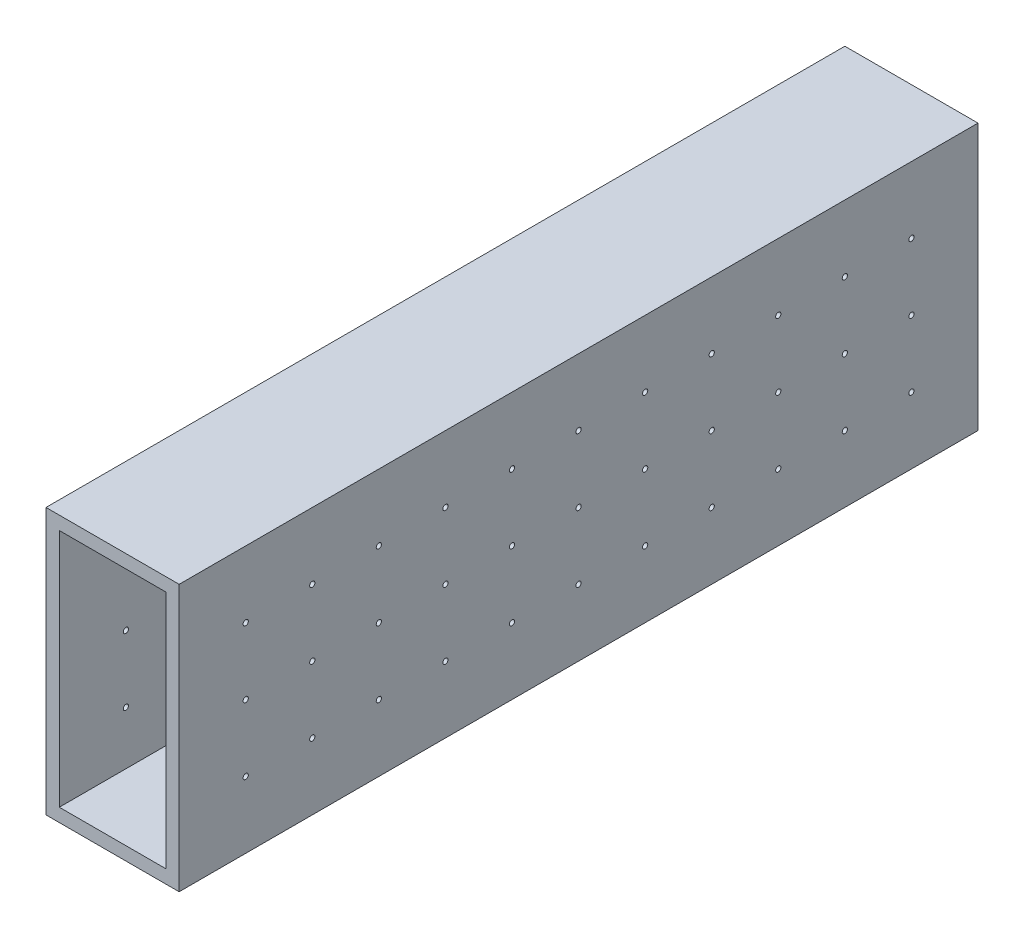
SolidWorks part; units mm, degrees
ref_plane "Front Plane" through (0, 0, 0) normal (0, 0, 1) x (1, 0, 0)
ref_plane "Top Plane" through (0, 0, 0) normal (0, 1, 0) x (1, 0, 0)
ref_plane "Right Plane" through (0, 0, 0) normal (1, 0, 0) x (0, 0, -1)
sketch "Sketch1" plane through (0, 0, 0) normal (0, 0, 1) x (1, 0, 0)
  line L1 (9.5125, 45.3382) -> (29.8325, 45.3382)
  line L2 (9.5125, 45.3382) -> (9.5125, -0.3818)
  line L3 (9.5125, -0.3818) -> (29.8325, -0.3818)
  line L4 (29.8325, 45.3382) -> (29.8325, -0.3818)
  line L5 (6.9725, 47.8782) -> (32.3725, 47.8782)
  line L6 (6.9725, 47.8782) -> (6.9725, -2.9218)
  line L7 (6.9725, -2.9218) -> (32.3725, -2.9218)
  line L8 (32.3725, 47.8782) -> (32.3725, -2.9218)
  dimension "D1" = 50.8
  dimension "D2" = 25.4
  dimension "D3" = 2.54
  dimension "D4" = 2.54
  dimension "D5" = 2.54
  dimension "D6" = 2.54
extrude "Boss-Extrude1" add sketch "Sketch1" along normal blind 152.4
sketch "Sketch2" plane through (32.3725, 0, 0) normal (1, 0, 0) x (0, 0, -1)
  line L0 (-152.4, -2.9218) -> (-152.4, 47.8782) construction
  line L1 (-152.4, 47.8782) -> (0, 47.8782) construction
  circle A0 centre (-139.7, 35.1782) radius 0.5
  circle A1 centre (-127, 35.1782) radius 0.5
  circle A2 centre (-114.3, 35.1782) radius 0.5
  circle A3 centre (-101.6, 35.1782) radius 0.5
  circle A4 centre (-88.9, 35.1782) radius 0.5
  circle A5 centre (-76.2, 35.1782) radius 0.5
  circle A6 centre (-63.5, 35.1782) radius 0.5
  circle A7 centre (-50.8, 35.1782) radius 0.5
  circle A8 centre (-38.1, 35.1782) radius 0.5
  circle A9 centre (-25.4, 35.1782) radius 0.5
  circle A10 centre (-12.7, 35.1782) radius 0.5
  circle A11 centre (-127, 22.4782) radius 0.5
  circle A12 centre (-114.3, 22.4782) radius 0.5
  circle A13 centre (-101.6, 22.4782) radius 0.5
  circle A14 centre (-88.9, 22.4782) radius 0.5
  circle A15 centre (-76.2, 22.4782) radius 0.5
  circle A16 centre (-63.5, 22.4782) radius 0.5
  circle A17 centre (-50.8, 22.4782) radius 0.5
  circle A18 centre (-38.1, 22.4782) radius 0.5
  circle A19 centre (-25.4, 22.4782) radius 0.5
  circle A20 centre (-12.7, 22.4782) radius 0.5
  circle A21 centre (-127, 9.7782) radius 0.5
  circle A22 centre (-114.3, 9.7782) radius 0.5
  circle A23 centre (-101.6, 9.7782) radius 0.5
  circle A24 centre (-88.9, 9.7782) radius 0.5
  circle A25 centre (-76.2, 9.7782) radius 0.5
  circle A26 centre (-63.5, 9.7782) radius 0.5
  circle A27 centre (-50.8, 9.7782) radius 0.5
  circle A28 centre (-38.1, 9.7782) radius 0.5
  circle A29 centre (-25.4, 9.7782) radius 0.5
  circle A30 centre (-12.7, 9.7782) radius 0.5
  circle A31 centre (-139.7, 22.4782) radius 0.5
  circle A32 centre (-139.7, 9.7782) radius 0.5
  dimension "D1" = 1
  dimension "D2" = 12.7
  dimension "D3" = 12.7
  dimension "D4" = 11
  dimension "D5" = 3
extrude "Cut-Extrude1" cut sketch "Sketch2" against normal through all both and the other way through all
